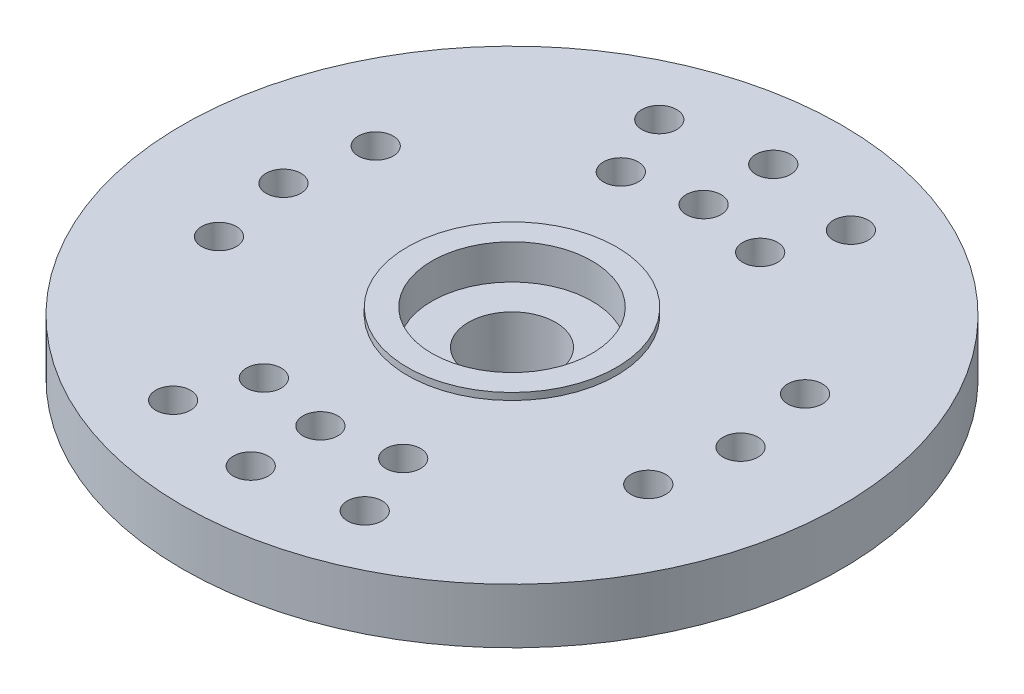
SolidWorks part; units mm, degrees
material "ABS"
ref_plane "Front Plane" through (0, 0, 0) normal (0, 0, 1) x (1, 0, 0)
ref_plane "Top Plane" through (0, 0, 0) normal (0, 1, 0) x (1, 0, 0)
ref_plane "Right Plane" through (0, 0, 0) normal (1, 0, 0) x (0, 0, -1)
sketch "Sketch1" plane through (0, 0, 0) normal (0, 0, 1) x (1, 0, 0)
  line L0 (0, 0) -> (0, 4.445)
  line L1 (0, 4.445) -> (3.81, 4.445)
  line L2 (3.81, 4.445) -> (3.81, 4.191)
  line L3 (3.81, 4.191) -> (12.0142, 4.191)
  line L4 (12.0142, 4.191) -> (12.0142, 2.1844)
  line L5 (12.0142, 2.1844) -> (4.5212, 2.1844)
  line L6 (4.5212, 2.1844) -> (4.5212, 0)
  line L7 (4.5212, 0) -> (0, 0)
  dimension "D1" = 4.445
  dimension "D2" = 3.81
  dimension "D3" = 4.5212
  dimension "D4" = 12.0142
  dimension "D5" = 2.0066
  dimension "D6" = 0.254
revolve "Revolve1" add sketch "Sketch1" angle 360 about L0
sketch "Sketch2" plane through (0, 4.445, 0) normal (0, 1, 0) x (1, 0, 0)
  circle A0 centre (0, 0) radius 2.921
  dimension "D1" = 5.842
extrude "Extrude1" cut sketch "Sketch2" against normal blind 1.27
sketch "Sketch3" plane through (0, 0, 0) normal (0, -1, 0) x (1, 0, 0)
  circle A0 centre (0, 0) radius 1.5875
  dimension "D1" = 3.175
extrude "Extrude2" cut sketch "Sketch3" against normal through all
sketch "Sketch4" plane through (0, 4.191, 0) normal (0, 1, 0) x (1, 0, 0)
  line L0 (0, 0) -> (8.3312, 0) construction
  line L1 (0, 0) -> (-8.3312, 0) construction
  line L2 (0, 0) -> (-7.8258, 2.8575) construction
  line L3 (-7.8258, 2.8575) -> (-7.8258, -2.8575) construction
  line L4 (-7.8258, -2.8575) -> (0, 0) construction
  line L5 (0, 0) -> (7.8258, 2.8575) construction
  line L6 (7.8258, 2.8575) -> (7.8258, -2.8575) construction
  line L7 (0, 0) -> (7.8258, -2.8575) construction
  line L8 (0, 0) -> (0, 6.985) construction
  line L9 (0, 0) -> (0, -6.985) construction
  line L10 (0, 0) -> (-2.54, 6.5068) construction
  line L11 (-2.54, 6.5068) -> (2.54, 6.5068) construction
  line L12 (2.54, 6.5068) -> (0, 0) construction
  line L13 (0, 0) -> (-2.54, -6.5068) construction
  line L14 (-2.54, -6.5068) -> (2.54, -6.5068) construction
  line L15 (2.54, -6.5068) -> (0, 0) construction
  circle A0 centre (0, 0) radius 8.3312 construction
  circle A1 centre (0, 0) radius 6.985 construction
  circle A2 centre (0, 6.985) radius 0.635
  circle A3 centre (-7.8258, 2.8575) radius 0.635
  circle A4 centre (-8.3312, 0) radius 0.635
  circle A5 centre (-7.8258, -2.8575) radius 0.635
  circle A6 centre (7.8258, 2.8575) radius 0.635
  circle A7 centre (8.3312, 0) radius 0.635
  circle A8 centre (7.8258, -2.8575) radius 0.635
  circle A9 centre (2.54, 6.5068) radius 0.635
  circle A10 centre (-2.54, 6.5068) radius 0.635
  circle A11 centre (2.54, -6.5068) radius 0.635
  circle A12 centre (0, -6.985) radius 0.635
  circle A13 centre (-2.54, -6.5068) radius 0.635
  dimension "D1" = 16.6624
  dimension "D2" = 13.97
  dimension "D3" = 1.27
  dimension "D4" = 5.715
  dimension "D5" = 5.715
  dimension "D6" = 5.08
  dimension "D7" = 5.08
extrude "Extrude3" cut sketch "Sketch4" against normal through all
sketch "Sketch5" plane through (0, 4.191, 0) normal (0, 1, 0) x (1, 0, 0)
  line L0 (0, 0) -> (0, 9.525) construction
  line L1 (0, 0) -> (0, -9.525) construction
  line L2 (0, 0) -> (3.4925, 8.8616) construction
  line L3 (3.4925, 8.8616) -> (-3.4925, 8.8616) construction
  line L4 (-3.4925, 8.8616) -> (0, 0) construction
  line L5 (0, 0) -> (3.4925, -8.8616) construction
  line L6 (3.4925, -8.8616) -> (-3.4925, -8.8616) construction
  line L7 (-3.4925, -8.8616) -> (0, 0) construction
  circle A0 centre (0, 0) radius 9.525 construction
  circle A1 centre (0, 9.525) radius 0.635
  circle A2 centre (3.4925, 8.8616) radius 0.635
  circle A3 centre (-3.4925, 8.8616) radius 0.635
  circle A4 centre (3.4925, -8.8616) radius 0.635
  circle A5 centre (0, -9.525) radius 0.635
  circle A6 centre (-3.4925, -8.8616) radius 0.635
  dimension "D1" = 19.05
  dimension "D3" = 1.27
  dimension "D2" = 6.985
extrude "Extrude4" cut sketch "Sketch5" against normal through all
